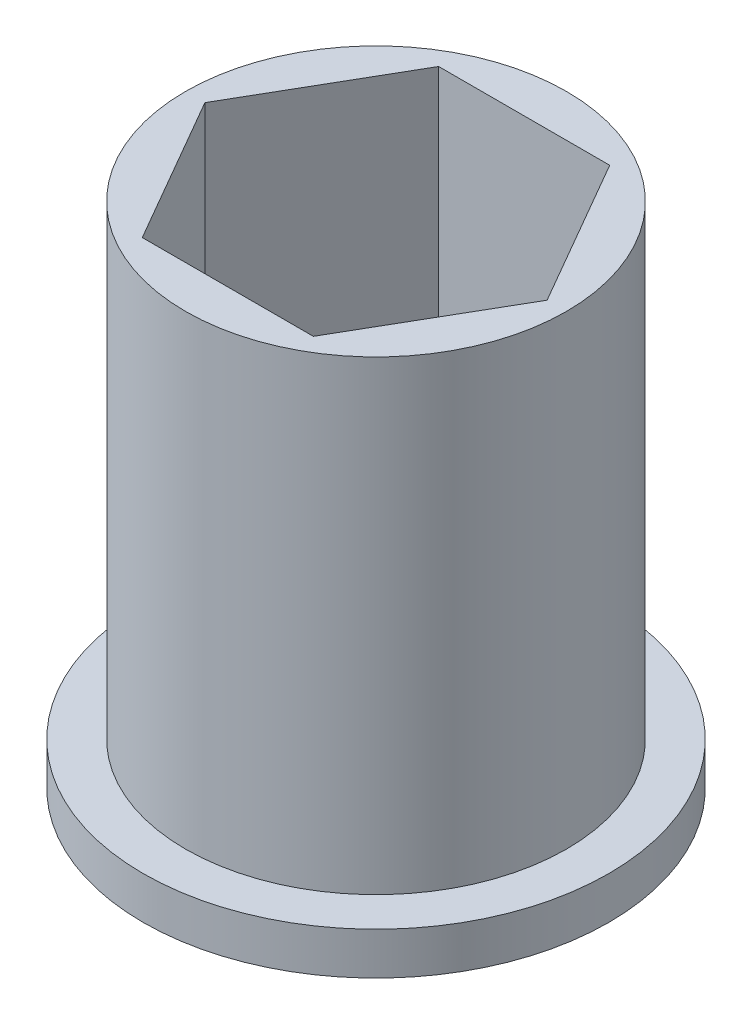
SolidWorks part; units mm, degrees
ref_plane "Front Plane" through (0, 0, 0) normal (0, 0, 1) x (1, 0, 0)
ref_plane "Top Plane" through (0, 0, 0) normal (0, 1, 0) x (1, 0, 0)
ref_plane "Right Plane" through (0, 0, 0) normal (1, 0, 0) x (0, 0, -1)
sketch "Sketch2" plane through (0, 0, 0) normal (0, 1, 0) x (1, 0, 0)
  line L1 (4.0415, 0) -> (2.0207, 3.5)
  line L2 (2.0207, 3.5) -> (-2.0207, 3.5)
  line L3 (-2.0207, 3.5) -> (-4.0415, 0)
  line L4 (-4.0415, 0) -> (-2.0207, -3.5)
  line L5 (-2.0207, -3.5) -> (2.0207, -3.5)
  line L6 (2.0207, -3.5) -> (4.0415, 0)
  circle A0 centre (0, 0) radius 4.5
  circle A1 centre (0, 0) radius 3.5 construction
  dimension "D1" = 9
  dimension "D2" = 7
extrude "Boss-Extrude1" add sketch "Sketch2" along normal blind 12
ref_plane "Plane1" through (0, 6, 0) normal (0, -1, 0) x (-1, 0, 0)
sketch "Sketch3" plane through (0, 6, 0) normal (0, -1, 0) x (-1, 0, 0)
  circle A0 centre (0, 0) radius 4.5 construction
  circle A1 centre (0, 0) radius 4.5
  circle A2 centre (0, 0) radius 5.5
  dimension "D1" = 1
sketch "Sketch4" plane through (0, 0, 0) normal (0, -1, 0) x (1, 0, 0)
  circle A0 centre (0, 0) radius 4.5 construction
  circle A2 centre (0, 0) radius 4.5
  circle A4 centre (0, 0) radius 5.5
  dimension "D1" = 1
extrude "Boss-Extrude3" add sketch "Sketch4" against normal blind 1
